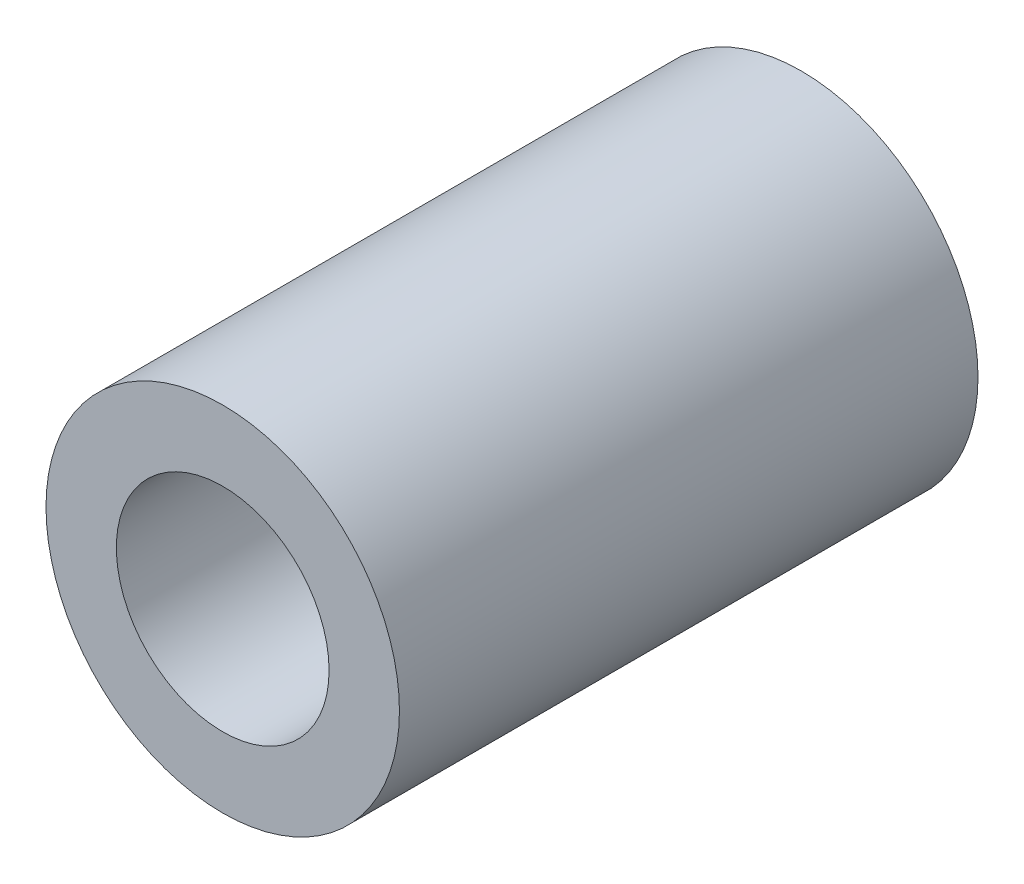
SolidWorks part; units mm, degrees
ref_plane "Front Plane" through (0, 0, 0) normal (0, 0, 1) x (1, 0, 0)
ref_plane "Top Plane" through (0, 0, 0) normal (0, 1, 0) x (1, 0, 0)
ref_plane "Right Plane" through (0, 0, 0) normal (1, 0, 0) x (0, 0, -1)
sketch "Sketch1" plane through (0, 0, 0) normal (0, 0, 1) x (1, 0, 0)
  circle A0 centre (0, 0) radius 7.9756
  circle A1 centre (0, 0) radius 4.8006
  dimension "D1" = 15.9512
  dimension "D2" = 3.175
  dimension "D3" = 9.6012
extrude "Boss-Extrude1" add sketch "Sketch1" along normal blind 26.1112
